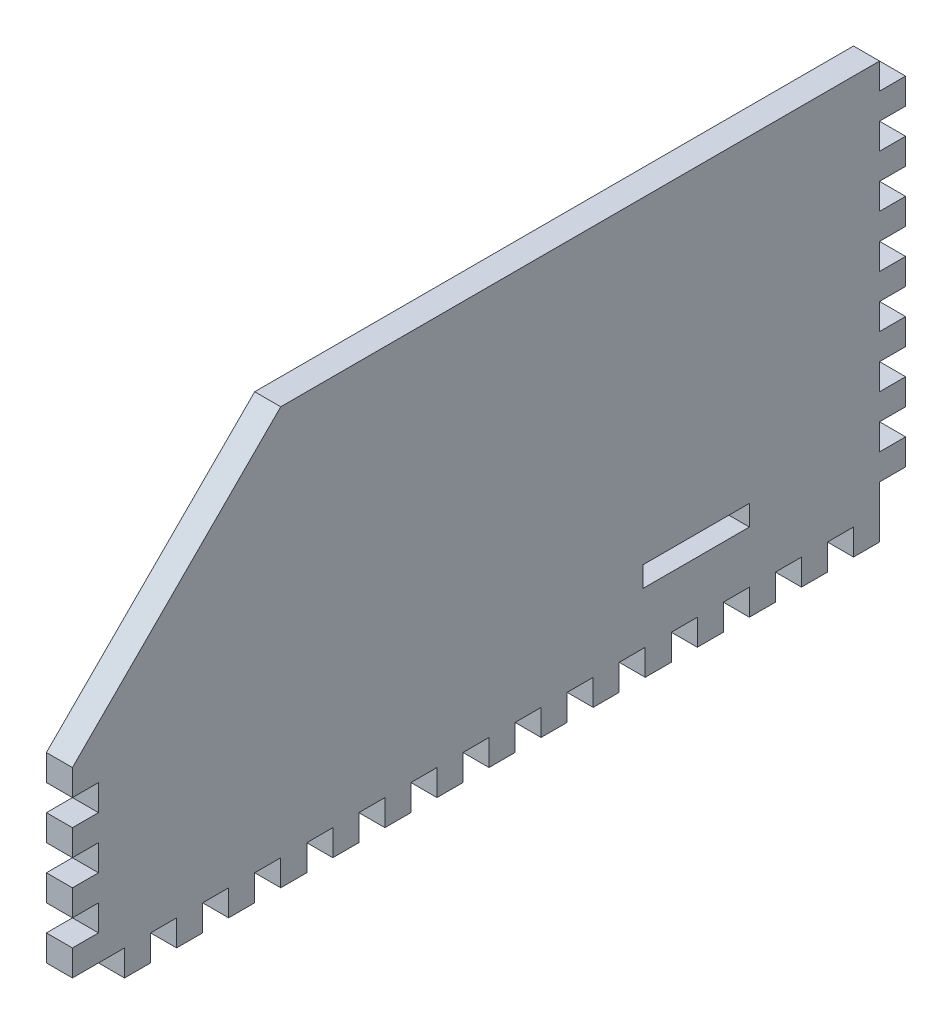
SolidWorks part; units mm, degrees
ref_plane "Front Plane" through (0, 0, 0) normal (0, 0, 1) x (1, 0, 0)
ref_plane "Top Plane" through (0, 0, 0) normal (0, 1, 0) x (1, 0, 0)
ref_plane "Right Plane" through (0, 0, 0) normal (1, 0, 0) x (0, 0, -1)
sketch "Sketch1" plane through (0, 0, 0) normal (1, 0, 0) x (0, 0, -1)
  line L1 (0, 0) -> (203.2, 0)
  line L2 (0, 0) -> (0, 101.6)
  line L3 (0, 101.6) -> (203.2, 101.6)
  line L4 (203.2, 0) -> (203.2, 101.6)
  dimension "D1" = 203.2
  dimension "D2" = 101.6
extrude "Boss-Extrude1" add sketch "Sketch1" along normal blind 6.35 contours L2 L3 L4 L1
sketch "Sketch2" plane through (0, 0, 0) normal (0, -1, 0) x (1, 0, 0)
  line L0 (6.35, 0) -> (6.35, -203.2) construction
  line L1 (0, 0) -> (6.35, 0)
  line L2 (0, 0) -> (0, -12.7)
  line L3 (0, -12.7) -> (6.35, -12.7)
  line L4 (6.35, 0) -> (6.35, -12.7)
  dimension "D1" = 12.7
extrude "Cut-Extrude1" cut sketch "Sketch2" against normal blind 6.35
sketch "Sketch5" plane through (0, 0, 0) normal (0, -1, 0) x (1, 0, 0)
  line L0 (0, -12.7) -> (0, -203.2) construction
  line L1 (0, -19.05) -> (6.35, -19.05)
  line L2 (0, -19.05) -> (0, -25.4)
  line L3 (0, -25.4) -> (6.35, -25.4)
  line L4 (6.35, -19.05) -> (6.35, -25.4)
  line L5 (6.35, -12.7) -> (6.35, -203.2) construction
extrude "Cut-Extrude3" cut sketch "Sketch5" against normal blind 6.35
pattern_linear "LPattern1" count 15 spacing 12.7 along (0, 0, -1) of "Cut-Extrude3"
sketch "Sketch6" plane through (0, 0, -203.2) normal (0, 0, -1) x (-1, 0, 0)
  line L0 (0, 6.35) -> (0, 101.6) construction
  line L1 (-6.35, 6.35) -> (0, 6.35)
  line L2 (-6.35, 6.35) -> (-6.35, 12.7)
  line L3 (-6.35, 12.7) -> (0, 12.7)
  line L4 (0, 6.35) -> (0, 12.7)
  dimension "D1" = 6.35
extrude "Cut-Extrude4" cut sketch "Sketch6" against normal blind 6.35 contours L2 L3 L4 L1
sketch "Sketch7" plane through (0, 0, -203.2) normal (0, 0, -1) x (-1, 0, 0)
  line L0 (0, 12.7) -> (0, 101.6) construction
  line L1 (0, 19.05) -> (-6.35, 19.05)
  line L2 (0, 19.05) -> (0, 25.4)
  line L3 (0, 25.4) -> (-6.35, 25.4)
  line L4 (-6.35, 19.05) -> (-6.35, 25.4)
  line L5 (-6.35, 12.7) -> (-6.35, 101.6) construction
extrude "Cut-Extrude5" cut sketch "Sketch7" against normal blind 6.35
pattern_linear "LPattern2" count 7 spacing 12.7 along (0, 1, 0) of "Cut-Extrude5"
sketch "Sketch8" plane through (6.35, 0, 0) normal (1, 0, 0) x (0, 0, -1)
  line L2 (0, 101.6) -> (50.8, 101.6)
  line L3 (0, 101.6) -> (196.85, 101.6) construction
  line L4 (0, 101.6) -> (0, 50.8)
  line L5 (0, 6.35) -> (0, 101.6) construction
  line L6 (0, 50.8) -> (50.8, 101.6)
  dimension "D1" = 50.8
  dimension "D2" = 50.8
extrude "Cut-Extrude6" cut sketch "Sketch8" against normal blind 6.35 contours L2 L6 L4
sketch "Sketch9" plane through (0, 0, 0) normal (0, 0, 1) x (1, 0, 0)
  line L0 (6.35, 6.35) -> (6.35, 50.8) construction
  line L1 (6.35, 12.7) -> (0, 12.7)
  line L2 (6.35, 12.7) -> (6.35, 19.05)
  line L3 (6.35, 19.05) -> (0, 19.05)
  line L4 (0, 12.7) -> (0, 19.05)
  line L5 (0, 6.35) -> (0, 50.8) construction
extrude "Cut-Extrude7" cut sketch "Sketch9" against normal blind 6.35
pattern_linear "LPattern3" count 3 spacing 12.7 along (0, 1, 0) of "Cut-Extrude7"
sketch "Sketch10" plane through (6.35, 0, 0) normal (1, 0, 0) x (0, 0, -1)
  line L0 (152.4, 0) -> (158.75, 0) construction
  line L1 (139.2, 19.05) -> (165.1, 19.05)
  line L2 (139.2, 19.05) -> (139.2, 24.05)
  line L3 (139.2, 24.05) -> (165.1, 24.05)
  line L4 (165.1, 19.05) -> (165.1, 24.05)
  dimension "D1" = 5
  dimension "D2" = 25.9
  dimension "D3" = 38.1
  dimension "D4" = 19.05
extrude "Cut-Extrude8" cut sketch "Sketch10" against normal blind 6.35
